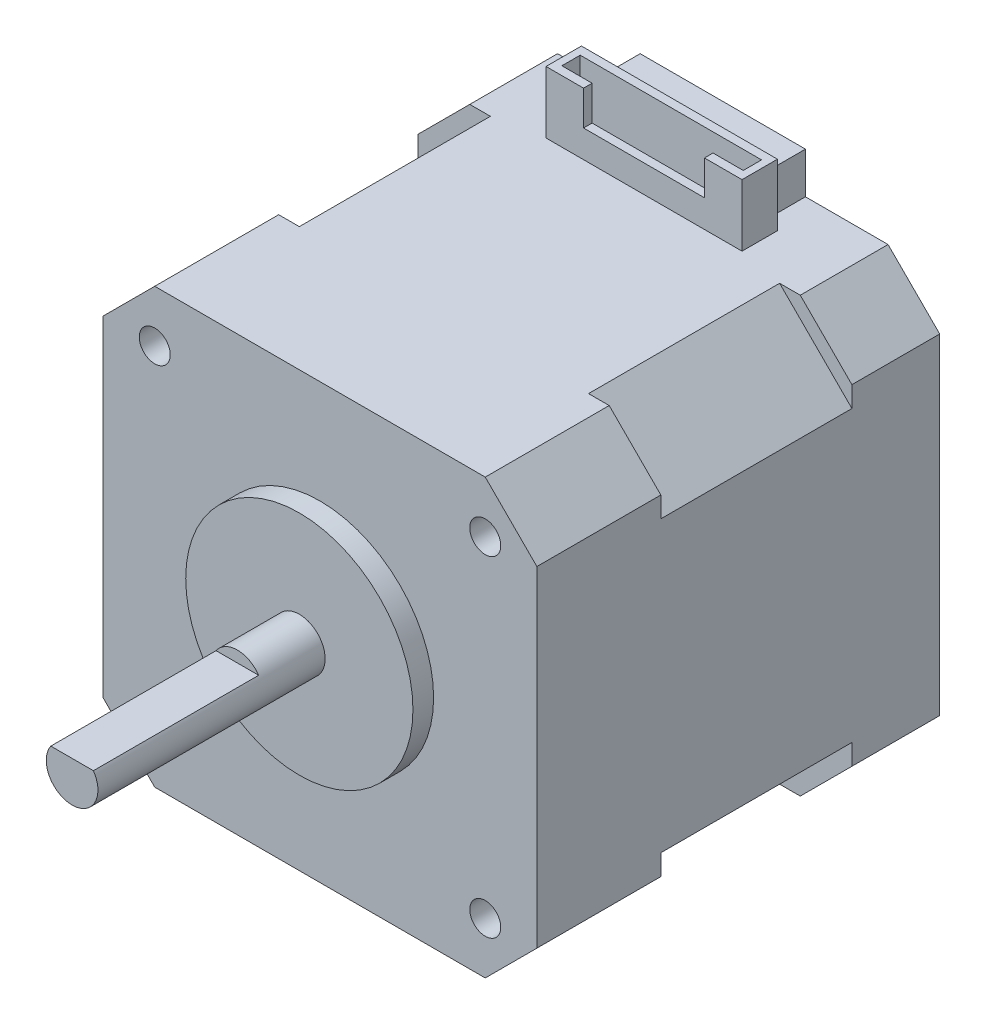
SolidWorks part; units mm, degrees
ref_plane "Front" through (0, 0, 0) normal (0, 0, 1) x (1, 0, 0)
ref_plane "Top" through (0, 0, 0) normal (0, 1, 0) x (1, 0, 0)
ref_plane "Right" through (0, 0, 0) normal (1, 0, 0) x (0, 0, -1)
sketch "草图1" plane through (0, 0, 0) normal (0, 0, 1) x (1, 0, 0)
  line L0 (0, 37) -> (5, 42)
  line L1 (5, 0) -> (37, 0)
  line L2 (0, 5) -> (0, 37)
  line L3 (5, 42) -> (37, 42)
  line L4 (42, 5) -> (42, 37)
  line L5 (42, 37) -> (37, 42)
  line L6 (37, 0) -> (42, 5)
  line L7 (5, 0) -> (0, 5)
  point P0 (0, 0)
  point P1 (42, 42)
  point P2 (0, 42)
  point P3 (42, 0)
extrude "凸台-拉伸1" add sketch "草图1" along normal blind 39 contours L3 L5 L4 L6 L1 L7 L2 L0
ref_plane "基准面1" through (0, 0, 27) normal (0, 0, 1) x (1, 0, 0)
sketch "草图2" plane through (0, 0, 27) normal (0, 0, 1) x (1, 0, 0)
  line L0 (37, 42) -> (35, 42)
  line L1 (5, 42) -> (37, 42) construction
  line L2 (42, 37) -> (42, 35)
  line L3 (42, 5) -> (42, 37) construction
  line L4 (35, 42) -> (42, 35)
  line L5 (37, 42) -> (42, 37)
  line L6 (42, 37) -> (37, 42) construction
  line L12 (5, 42) -> (0, 37)
  line L13 (7, 42) -> (0, 35)
  line L14 (0, 37) -> (0, 35)
  line L15 (5, 42) -> (7, 42)
  line L16 (5, 0) -> (7, 0)
  line L17 (0, 5) -> (0, 7)
  line L18 (7, 0) -> (0, 7)
  line L19 (5, 0) -> (0, 5)
  line L20 (37, 0) -> (42, 5)
  line L21 (35, 0) -> (42, 7)
  line L22 (42, 5) -> (42, 7)
  line L23 (37, 0) -> (35, 0)
extrude "切除-拉伸1" cut sketch "草图2" against normal blind 18.5
sketch "草图3" plane through (0, 0, 39) normal (0, 0, 1) x (1, 0, 0)
  circle A0 centre (21, 21) radius 11
extrude "凸台-拉伸2" add sketch "草图3" along normal blind 2
sketch "草图4" plane through (0, 0, 41) normal (0, 0, 1) x (1, 0, 0)
  circle A0 centre (21, 21) radius 2.5
extrude "凸台-拉伸3" add sketch "草图4" along normal blind 22 contours A0
sketch "草图5" plane through (0, 0, 63) normal (0, 0, 1) x (1, 0, 0)
  line L0 (18.9376, 22.4129) -> (23.0624, 22.4129)
  arc A0 (23.0624, 22.4129) -> (18.9376, 22.4129) centre (21, 21) ccw
extrude "切除-拉伸2" cut sketch "草图5" against normal blind 16
sketch "草图6" plane through (0, 0, 39) normal (0, 0, 1) x (1, 0, 0)
  circle A0 centre (37, 5) radius 1.5
  circle A1 centre (5, 5) radius 1.5
  circle A3 centre (37, 37) radius 1.5
  circle A4 centre (5, 37) radius 1.5
extrude "切除-拉伸3" cut sketch "草图6" against normal blind 5
sketch "草图7" plane through (0, 42, 0) normal (0, 1, 0) x (1, 0, 0)
  line L0 (5, 0) -> (37, 0) construction
  line L1 (29, 0) -> (13, 0)
  line L2 (29, 0) -> (29, -4.2)
  line L3 (29, -4.2) -> (13, -4.2)
  line L4 (13, 0) -> (13, -4.2)
  line L5 (42, -8.5) -> (42, 0) construction
  line L6 (0, -8.5) -> (0, 0) construction
  dimension "D1" = 13
  dimension "D2" = 13
extrude "凸台-拉伸4" add sketch "草图7" along normal blind 4
sketch "草图8" plane through (0, 42, 0) normal (0, 1, 0) x (1, 0, 0)
  line L1 (30.4893, -7.629) -> (11.5107, -7.629)
  line L2 (30.4893, -7.629) -> (30.4893, -4.2)
  line L3 (30.4893, -4.2) -> (11.5107, -4.2)
  line L4 (11.5107, -7.629) -> (11.5107, -4.2)
  line L5 (21, -4.2) -> (21, -7.629) construction
  line L6 (30.4893, -5.9145) -> (11.5107, -5.9145) construction
  line L7 (29.7798, -5.0276) -> (12.2202, -5.0276)
  line L8 (29.7798, -5.0276) -> (29.7798, -6.8013)
  line L9 (29.7798, -6.8013) -> (12.2202, -6.8013)
  line L10 (12.2202, -5.0276) -> (12.2202, -6.8013)
  line L11 (21, -6.8013) -> (21, -5.0276) construction
  line L12 (29.7798, -5.9145) -> (12.2202, -5.9145) construction
  point P0 (21, -5.9145)
  point P4 (21, -5.9145)
extrude "凸台-拉伸5" add sketch "草图8" along normal blind 6
sketch "草图9" plane through (0, 0, 7.629) normal (0, 0, 1) x (1, 0, 0)
  line L0 (11.5107, 48) -> (30.4893, 48) construction
  line L1 (26.8536, 44.6584) -> (15.1464, 44.6584)
  line L2 (26.8536, 44.6584) -> (26.8536, 48)
  line L3 (26.8536, 48) -> (15.1464, 48)
  line L4 (15.1464, 44.6584) -> (15.1464, 48)
  line L5 (21, 48) -> (21, 44.6584) construction
  line L6 (26.8536, 46.3292) -> (15.1464, 46.3292) construction
  point P0 (21, 46.3292)
extrude "切除-拉伸4" cut sketch "草图9" against normal blind 2 contours L4 L3 L2 L1
